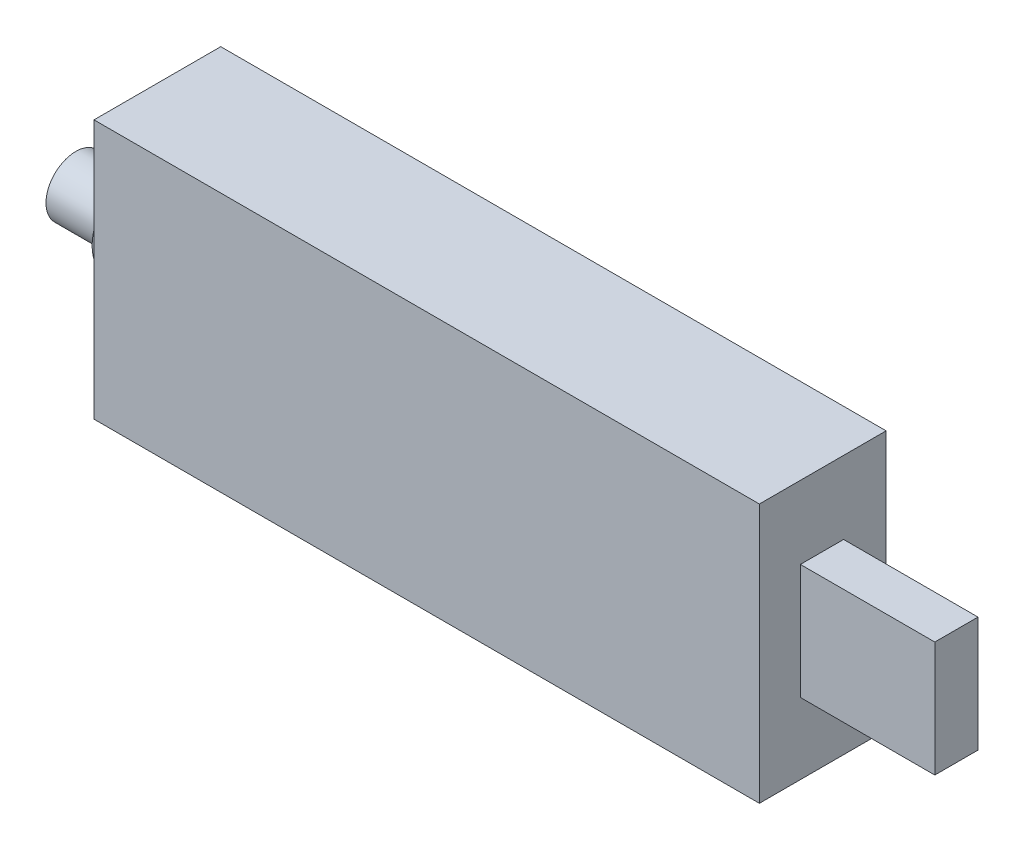
SolidWorks part; units mm, degrees
ref_plane "Front Plane" through (0, 0, 0) normal (0, 0, 1) x (1, 0, 0)
ref_plane "Top Plane" through (0, 0, 0) normal (0, 1, 0) x (1, 0, 0)
ref_plane "Right Plane" through (0, 0, 0) normal (1, 0, 0) x (0, 0, -1)
sketch "Sketch1" plane through (0, 0, 0) normal (0, 0, 1) x (1, 0, 0)
  line L1 (0, 0) -> (-69.3, 0)
  line L2 (0, 0) -> (0, 27)
  line L3 (0, 27) -> (-69.3, 27)
  line L4 (-69.3, 0) -> (-69.3, 27)
  dimension "D1" = 69.3
  dimension "D2" = 27
extrude "Boss-Extrude1" add sketch "Sketch1" along normal blind 13.2
sketch "Sketch2" plane through (-69.3, 0, 0) normal (-1, 0, 0) x (0, 0, 1)
  line L0 (6.6, 27) -> (6.6, 0) construction
  line L1 (13.2, 27) -> (0, 27) construction
  line L2 (13.2, 0) -> (0, 0) construction
  line L3 (0, 13.5) -> (13.2, 13.5) construction
  line L4 (0, 27) -> (0, 0) construction
  line L5 (13.2, 27) -> (13.2, 0) construction
  circle A0 centre (6.6, 13.5) radius 4.55
  dimension "D1" = 9.1
extrude "Boss-Extrude2" add sketch "Sketch2" along normal blind 2.25
sketch "Sketch3" plane through (-71.55, 0, 0) normal (-1, 0, 0) x (0, 0, 1)
  circle A0 centre (6.6, 13.5) radius 3.1
extrude "Boss-Extrude3" add sketch "Sketch3" along normal blind 6.25
sketch "Sketch4" plane through (0, 0, 0) normal (1, 0, 0) x (0, 0, -1)
  line L1 (-4.4301, 19.4149) -> (-8.9301, 19.4149)
  line L2 (-4.4301, 19.4149) -> (-4.4301, 7.4149)
  line L3 (-4.4301, 7.4149) -> (-8.9301, 7.4149)
  line L4 (-8.9301, 19.4149) -> (-8.9301, 7.4149)
  line L5 (-4.4301, 19.4149) -> (-8.9301, 7.4149) construction
  line L6 (-4.4301, 7.4149) -> (-8.9301, 19.4149) construction
  point P0 (-6.6801, 13.4149)
  dimension "D1" = 12
  dimension "D2" = 4.5
extrude "Boss-Extrude4" add sketch "Sketch4" along normal blind 14
